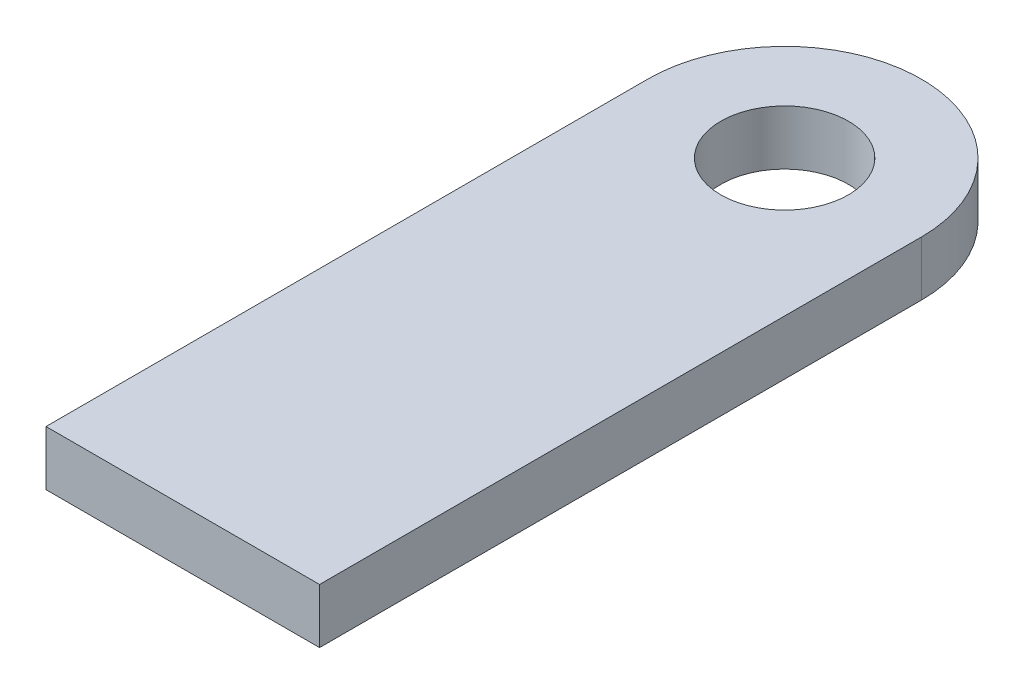
SolidWorks part; units mm, degrees
ref_plane "Front Plane" through (0, 0, 0) normal (0, 0, 1) x (1, 0, 0)
ref_plane "Top Plane" through (0, 0, 0) normal (0, 1, 0) x (1, 0, 0)
ref_plane "Right Plane" through (0, 0, 0) normal (1, 0, 0) x (0, 0, -1)
sketch "Sketch1" plane through (0, 0, 0) normal (0, 1, 0) x (1, 0, 0)
  line L0 (-8.7117, 0.1756) -> (-8.7117, 33.1756)
  line L1 (6.2883, 33.1756) -> (6.2883, 0.1756)
  line L2 (6.2883, 0.1756) -> (-8.7117, 0.1756)
  arc A0 (-8.7117, 33.1756) -> (6.2883, 33.1756) centre (-1.2117, 33.1756) cw
  circle A1 centre (-1.2117, 33.1756) radius 3.5
  dimension "D1" = 7
  dimension "D3" = 33
  dimension "D2" = 15
extrude "Boss-Extrude1" add sketch "Sketch1" along normal blind 3
